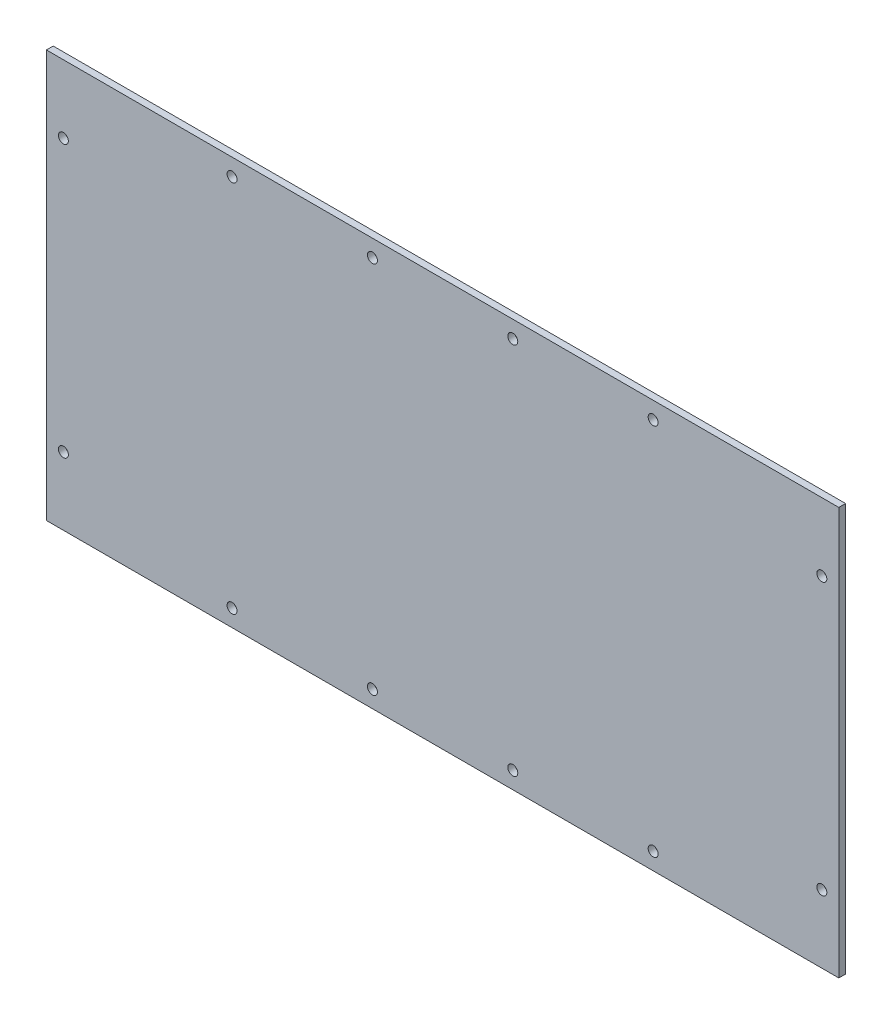
SolidWorks part; units mm, degrees
ref_plane "正面" through (0, 0, 0) normal (0, 0, 1) x (1, 0, 0)
ref_plane "平面" through (0, 0, 0) normal (0, 1, 0) x (1, 0, 0)
ref_plane "右側面" through (0, 0, 0) normal (1, 0, 0) x (0, 0, -1)
sketch "ｽｹｯﾁ1" plane through (0, 0, 0) normal (0, 0, 1) x (1, 0, 0)
  line L1 (-175, 90) -> (175, 90)
  line L2 (-175, 90) -> (-175, -90)
  line L3 (-175, -90) -> (175, -90)
  line L4 (175, 90) -> (175, -90)
  line L5 (-175, 90) -> (175, -90) construction
  line L6 (-175, -90) -> (175, 90) construction
  point P0 (0, 0)
  dimension "D1" = 180
  dimension "D2" = 350
extrude "ﾎﾞｽ - 押し出し1" add sketch "ｽｹｯﾁ1" along normal blind 3
sketch "ｽｹｯﾁ2" plane through (0, 0, 3) normal (0, 0, 1) x (1, 0, 0)
  line L1 (175, 90) -> (167.5, 90)
  line L2 (175, 90) -> (175, 60)
  line L3 (175, 60) -> (167.5, 60)
  line L4 (167.5, 90) -> (167.5, 60)
  line L5 (175, -90) -> (167.5, -90)
  line L6 (175, -90) -> (175, -60)
  line L7 (175, -60) -> (167.5, -60)
  line L8 (167.5, -90) -> (167.5, -60)
  line L9 (-175, 90) -> (-167.5, 90)
  line L10 (-175, 90) -> (-175, 60)
  line L11 (-175, 60) -> (-167.5, 60)
  line L12 (-167.5, 90) -> (-167.5, 60)
  line L13 (-175, -90) -> (-167.5, -90)
  line L14 (-175, -90) -> (-175, -60)
  line L15 (-175, -60) -> (-167.5, -60)
  line L16 (-167.5, -90) -> (-167.5, -60)
  circle A0 centre (167.5, -60) radius 2.2
  circle A1 centre (167.5, 60) radius 2.2
  circle A2 centre (-167.5, 60) radius 2.2
  circle A3 centre (-167.5, -60) radius 2.2
  dimension "D5" = 4.4
  dimension "D6" = 4.4
  dimension "D11" = 4.4
  dimension "D12" = 4.4
  dimension "D1" = 7.5
  dimension "D2" = 30
  dimension "D3" = 30
  dimension "D4" = 7.5
  dimension "D7" = 7.5
  dimension "D8" = 7.5
  dimension "D9" = 30
  dimension "D10" = 30
extrude "ｶｯﾄ - 押し出し1" cut sketch "ｽｹｯﾁ2" against normal blind 140 contours L4 A1 L3 | L3 A1 L4 | L7 A0 L8 | L8 A0 L7 | L11 A2 L12 | L12 A2 L11 | L16 A3 L15 | L15 A3 L16
sketch "ｽｹｯﾁ3" plane through (0, 0, 3) normal (0, 0, 1) x (1, 0, 0)
  line L0 (175, 90) -> (175, 82.5)
  line L1 (175, -90) -> (175, 90) construction
  line L2 (175, 82.5) -> (93, 82.5)
  line L3 (93, 82.5) -> (31, 82.5)
  line L4 (31, 82.5) -> (-31, 82.5)
  line L5 (-31, 82.5) -> (-93, 82.5)
  circle A1 centre (93, 82.5) radius 2.2
  circle A2 centre (31, 82.5) radius 2.2
  circle A3 centre (-31, 82.5) radius 2.2
  circle A4 centre (-93, 82.5) radius 2.2
  dimension "D6" = 4.4
  dimension "D7" = 4.4
  dimension "D8" = 4.4
  dimension "D9" = 4.4
  dimension "D1" = 7.5
  dimension "D2" = 82
  dimension "D3" = 62
  dimension "D4" = 62
  dimension "D5" = 62
extrude "ｶｯﾄ - 押し出し2" cut sketch "ｽｹｯﾁ3" against normal blind 310
sketch "ｽｹｯﾁ4" plane through (0, 0, 3) normal (0, 0, 1) x (1, 0, 0)
  line L0 (175, -90) -> (175, -82.5)
  line L1 (175, -90) -> (175, 90) construction
  line L2 (175, -82.5) -> (93, -82.5)
  line L3 (93, -82.5) -> (31, -82.5)
  line L4 (31, -82.5) -> (-31, -82.5)
  line L5 (-31, -82.5) -> (-93, -82.5)
  circle A0 centre (93, -82.5) radius 2.2
  circle A1 centre (31, -82.5) radius 2.2
  circle A2 centre (-31, -82.5) radius 2.2
  circle A4 centre (-93, -82.5) radius 2.2
  point P13 (0, 0)
  dimension "D6" = 4.4
  dimension "D7" = 4.4
  dimension "D8" = 4.4
  dimension "D9" = 4.4
  dimension "D1" = 7.5
  dimension "D2" = 82
  dimension "D3" = 62
  dimension "D4" = 62
  dimension "D5" = 62
extrude "ｶｯﾄ - 押し出し3" cut sketch "ｽｹｯﾁ4" against normal blind 310
